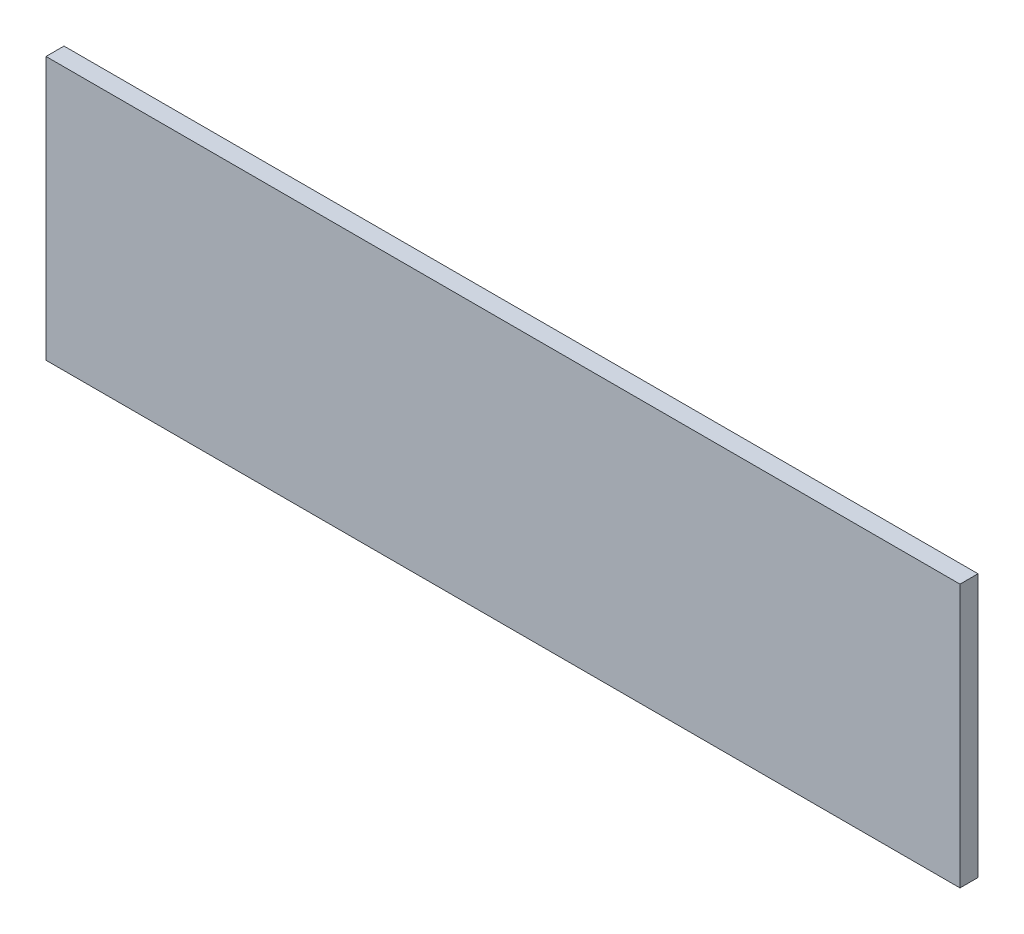
SolidWorks part; units mm, degrees
ref_plane "Front Plane" through (0, 0, 0) normal (0, 0, 1) x (1, 0, 0)
ref_plane "Top Plane" through (0, 0, 0) normal (0, 1, 0) x (1, 0, 0)
ref_plane "Right Plane" through (0, 0, 0) normal (1, 0, 0) x (0, 0, -1)
sketch "Sketch1" plane through (0, 0, 0) normal (0, 0, 1) x (1, 0, 0)
  line L0 (330, 0) -> (330, 200) construction
  line L1 (0, 200) -> (330, 200)
  line L2 (0, 200) -> (0, 105)
  line L3 (0, 105) -> (330, 105)
  line L4 (330, 200) -> (330, 105)
extrude "Boss-Extrude1" add sketch "Sketch1" along normal blind 6.5
